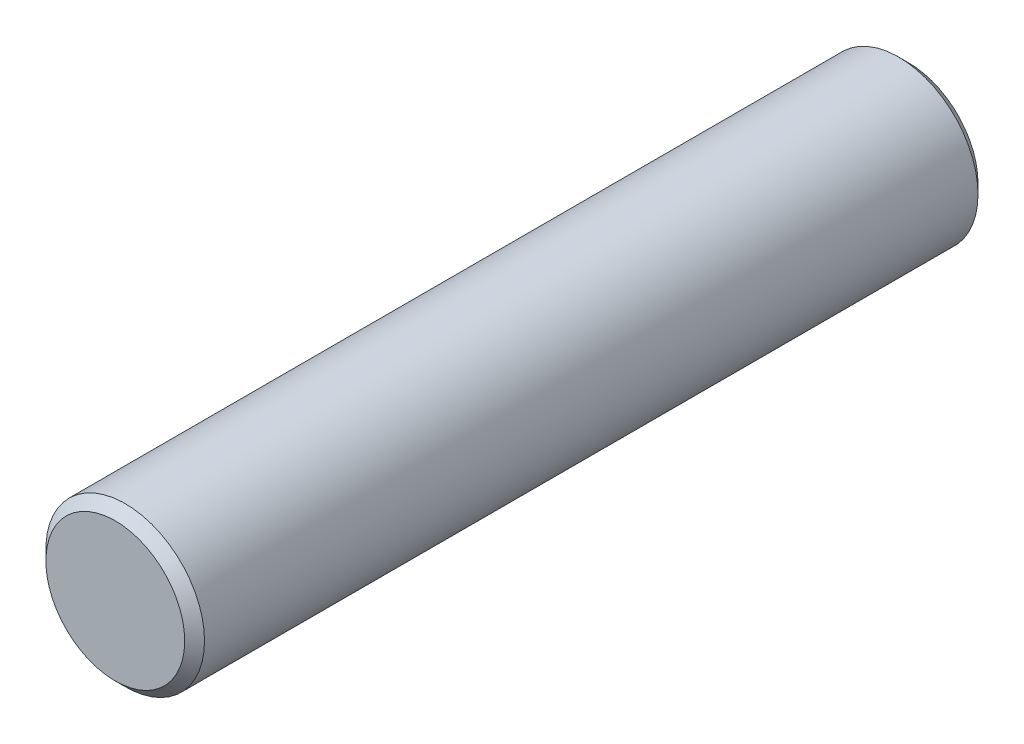
SolidWorks part; units mm, degrees
ref_plane "前视基准面" through (0, 0, 0) normal (0, 0, 1) x (1, 0, 0)
ref_plane "上视基准面" through (0, 0, 0) normal (0, 1, 0) x (1, 0, 0)
ref_plane "右视基准面" through (0, 0, 0) normal (1, 0, 0) x (0, 0, -1)
sketch "草图1" plane through (0, 0, 0) normal (0, 0, 1) x (1, 0, 0)
  circle A0 centre (0, 0) radius 4
extrude "凸台-拉伸1" add sketch "草图1" along normal blind 40
chamfer "倒角1" distance 0.5 angle 45 2 edges at (4, 0, 0) (4, 0, 40)
